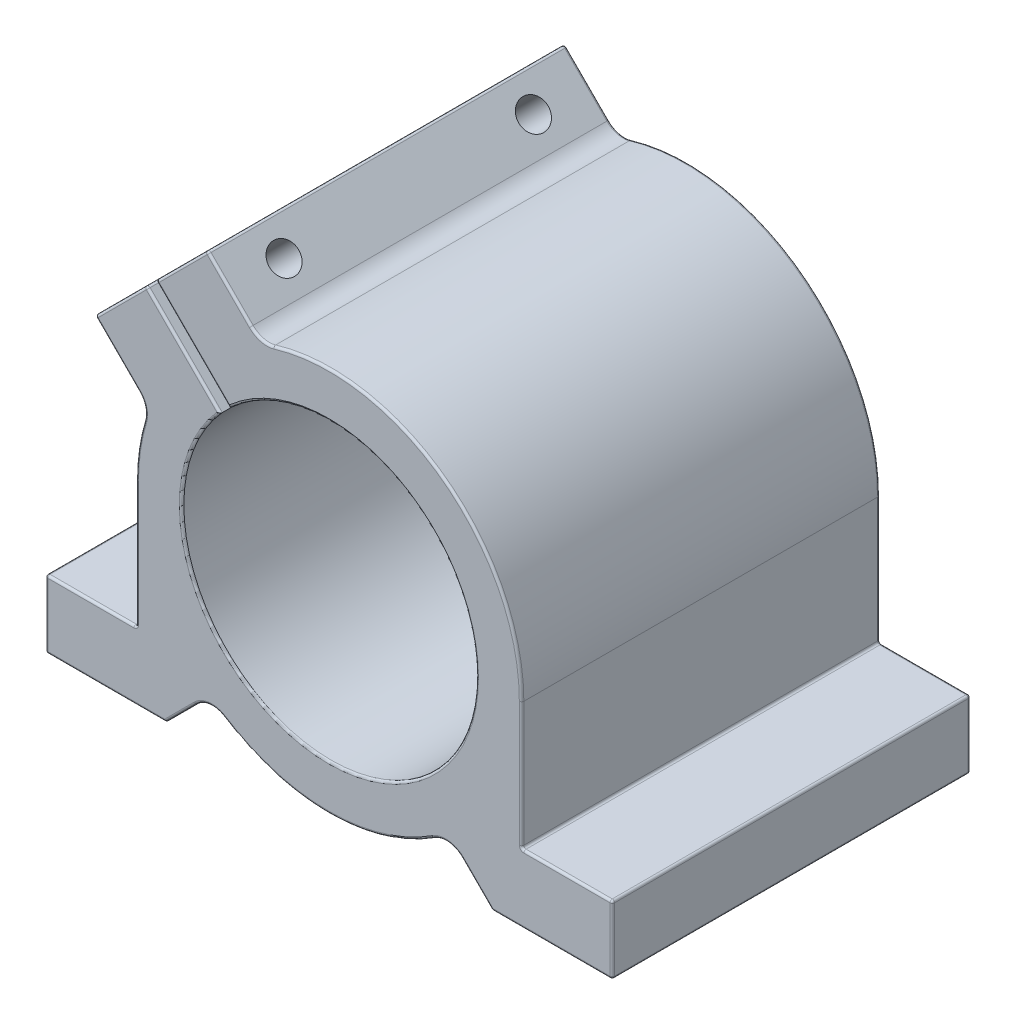
SolidWorks part; units mm, degrees
ref_plane "Спереди" through (0, 0, 0) normal (0, 0, 1) x (1, 0, 0)
ref_plane "Сверху" through (0, 0, 0) normal (0, 1, 0) x (1, 0, 0)
ref_plane "Справа" through (0, 0, 0) normal (1, 0, 0) x (0, 0, -1)
sketch "Эскиз1" plane through (0, 0, 0) normal (0, 0, 1) x (1, 0, 0)
  line L0 (0, 0) -> (0, -43) construction
  line L1 (62.5, -43) -> (-62.5, -43)
  line L2 (145.9589, 387.2071) -> (979.2922, 387.2071) construction
  line L3 (-62.5, -43) -> (-62.5, -28)
  line L4 (-62.5, -28) -> (-42.5, -28)
  line L5 (-42.5, -28) -> (-42.5, 0)
  line L6 (12.3744, 12.3744) -> (-12.3744, -12.3744)
  line L7 (12.3744, 12.3744) -> (-26.8456, 51.5943)
  line L8 (-12.3744, -12.3744) -> (-51.5943, 26.8456)
  line L9 (-26.8456, 51.5943) -> (-51.5943, 26.8456)
  line L10 (0, 0) -> (-39.2199, 39.2199) construction
  line L11 (1.0607, 1.0607) -> (-38.1593, 40.2806)
  line L12 (-1.0607, -1.0607) -> (-40.2806, 38.1593)
  line L13 (42.5, -28) -> (42.5, 0)
  line L14 (62.5, -28) -> (42.5, -28)
  line L15 (-36, -43) -> (-26.3475, -33.3475)
  line L16 (36, -43) -> (26.3475, -33.3475)
  line L17 (62.5, -43) -> (62.5, -28)
  circle A0 centre (0, 0) radius 32.5
  circle A1 centre (0, 0) radius 42.5
  point P20 (-24.0171, 21.8958)
  dimension "D1" = 65
  dimension "D2" = 43
  dimension "D3" = 125
  dimension "D4" = 20
  dimension "D5" = 15
  dimension "D6" = 35
  dimension "D9" = 45
  dimension "D10" = 23
  dimension "D11" = 45
  dimension "D12" = 26.5
  dimension "D7" = 1.5
  dimension "D8" = 1.5
extrude "Бобышка-Вытянуть1" add sketch "Эскиз1" along normal mid plane 79 contours A1 L16 L1 L17 L14 L13 | A1 L7 A0 L8 | A1 L5 L4 L3 L1 L15 | L7 A1 L11 A0 | L12 A1 L8 A0 | A1 L12 L9 L8 | A1 L7 L9 L11
fillet "Скругление1" radius 5 4 edges at (26.3475, -33.3475, 0) (-26.3475, -33.3475, 0) (-39.7605, 15.0118, 0) (-15.0118, 39.7605, 0)
sketch "Эскиз2" plane through (12.3744, 12.3744, 0) normal (0.7071, 0.7071, 0) x (0, 0, -1)
  line L0 (-39.5, 48.4654) -> (39.5, 48.4654) construction
  line L1 (-39.5, 41.833) -> (-39.5, 55.4654) construction
  line L2 (39.5, 41.833) -> (39.5, 55.4654) construction
  line L3 (-39.5, 55.4654) -> (39.5, 55.4654) construction
  circle A0 centre (-27.5, 48.4654) radius 3.25
  circle A1 centre (27.5, 48.4654) radius 3.25
  dimension "D1" = 6.5
  dimension "D2" = 6.5
  dimension "D3" = 7
  dimension "D4" = 12
  dimension "D5" = 12
extrude "Вырез-Вытянуть1" cut sketch "Эскиз2" against normal up to surface (19 mm away) up to face at (-32.1489, 30.0275, 0)
sketch "Эскиз3" plane through (-1.0607, -1.0607, 0) normal (0.7071, 0.7071, 0) x (0, 0, -1)
  circle A0 centre (-27.5, 48.4654) radius 2.1
  circle A1 centre (27.5, 48.4654) radius 2.1
  dimension "D1" = 4.2
  dimension "D2" = 4.2
extrude "Вырез-Вытянуть2" cut sketch "Эскиз3" against normal through all
fillet "Скругление2" radius 0.5 60 edges at (-42.5, -28, 0) (-62.5, -28, 0) (-40.2806, 38.1593, 0) (-51.5943, 26.8456, 0) (-26.8456, 51.5943, 0) (-38.1593, 40.2806, 0) (62.5, -28, 0) (42.5, -28, 0) (-62.5, -43, 0) (-36, -43, 0) (36, -43, 0) (62.5, -43, 0) (25.3615, 34.1034, 39.5) (25.3615, 34.1034, -39.5) (-14.8917, 40.6417, 39.5) (-14.8917, 40.6417, -39.5) (-22.0258, 46.7745, 39.5) (-22.0258, 46.7745, -39.5) (-32.5024, 45.9375, -39.5) (-32.5024, 45.9375, 39.5) (-30.0275, 32.1489, -39.5) (-30.0275, 32.1489, 39.5) (22.981, -22.981, -39.5) (22.981, -22.981, 39.5) (-32.1489, 30.0275, -39.5) (-32.1489, 30.0275, 39.5) (-45.9375, 32.5024, -39.5) (-45.9375, 32.5024, 39.5) (-46.7745, 22.0258, -39.5) (-46.7745, 22.0258, 39.5) (-40.6417, 14.8917, 39.5) (-40.6417, 14.8917, -39.5) (-42.0481, 6.1815, 39.5) (-42.0481, 6.1815, -39.5) (-42.5, -14, -39.5) (-42.5, -14, 39.5) (-52.5, -28, -39.5) (-52.5, -28, 39.5) (-62.5, -35.5, -39.5) (-62.5, -35.5, 39.5) (-49.25, -43, 39.5) (-49.25, -43, -39.5) (-32.6712, -39.6712, -39.5) (-32.6712, -39.6712, 39.5) (-26.3335, -34.9058, 39.5) (-26.3335, -34.9058, -39.5) (0, -42.5, 39.5) (0, -42.5, -39.5) (26.3335, -34.9058, 39.5) (26.3335, -34.9058, -39.5) (32.6712, -39.6712, 39.5) (32.6712, -39.6712, -39.5) (49.25, -43, 39.5) (49.25, -43, -39.5) (62.5, -35.5, -39.5) (62.5, -35.5, 39.5) (52.5, -28, -39.5) (52.5, -28, 39.5) (42.5, -14, -39.5) (42.5, -14, 39.5)
